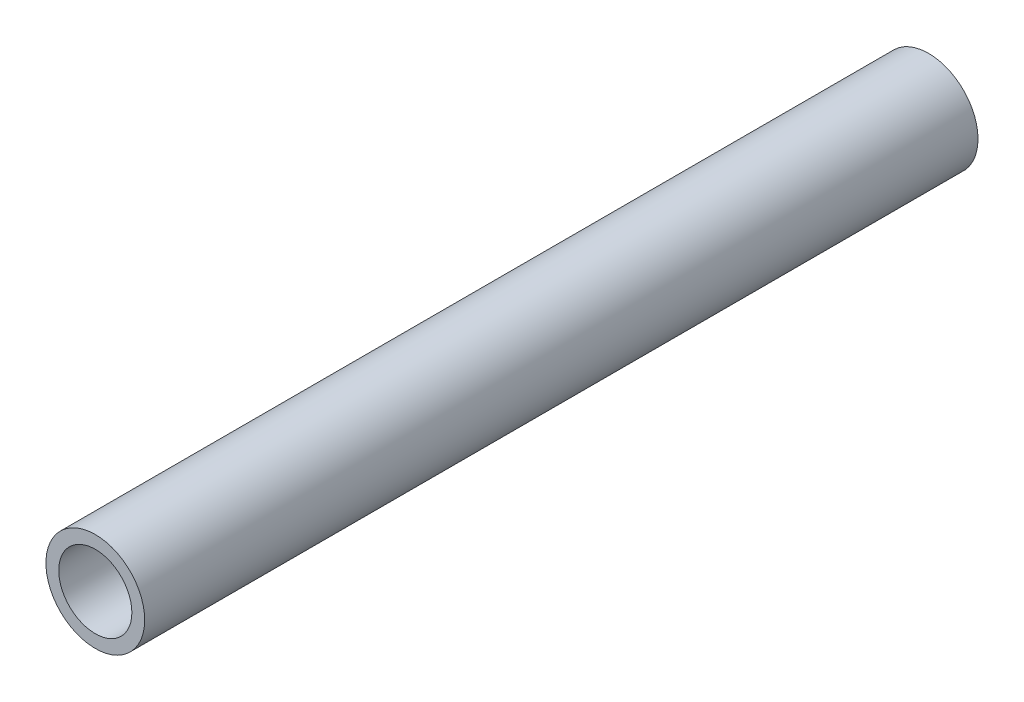
SolidWorks part; units mm, degrees
ref_plane "Front Plane" through (0, 0, 0) normal (0, 0, 1) x (1, 0, 0)
ref_plane "Top Plane" through (0, 0, 0) normal (0, 1, 0) x (1, 0, 0)
ref_plane "Right Plane" through (0, 0, 0) normal (1, 0, 0) x (0, 0, -1)
sketch "Sketch1" plane through (0, 0, 0) normal (0, 0, 1) x (1, 0, 0)
  circle A0 centre (0, 0) radius 10.668
  dimension "Pipe OD" = 21.336
extrude "Extrude-Thin1" add sketch "Sketch1" along normal mid plane 180 thin thin type one direction reverse wall 2.7686
